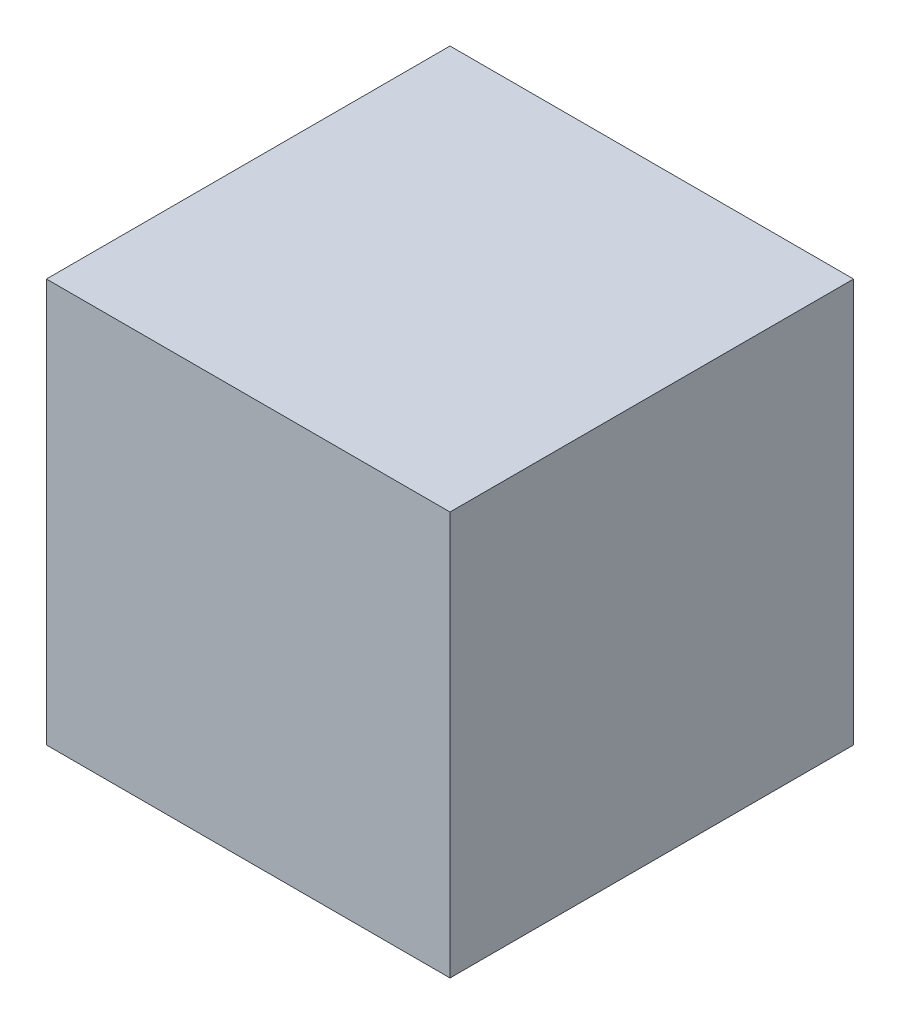
SolidWorks part; units mm, degrees
ref_plane "Front Plane" through (0, 0, 0) normal (0, 0, 1) x (1, 0, 0)
ref_plane "Top Plane" through (0, 0, 0) normal (0, 1, 0) x (1, 0, 0)
ref_plane "Right Plane" through (0, 0, 0) normal (1, 0, 0) x (0, 0, -1)
sketch "Sketch1" plane through (0, 0, 0) normal (0, 0, 1) x (1, 0, 0)
  line L1 (190.5, -190.5) -> (-190.5, -190.5)
  line L2 (190.5, -190.5) -> (190.5, 190.5)
  line L3 (190.5, 190.5) -> (-190.5, 190.5)
  line L4 (-190.5, -190.5) -> (-190.5, 190.5)
  line L5 (190.5, -190.5) -> (-190.5, 190.5) construction
  line L6 (190.5, 190.5) -> (-190.5, -190.5) construction
  point P0 (0, 0)
  dimension "D1" = 381
  dimension "D2" = 381
extrude "Boss-Extrude1" add sketch "Sketch1" along normal blind 381
